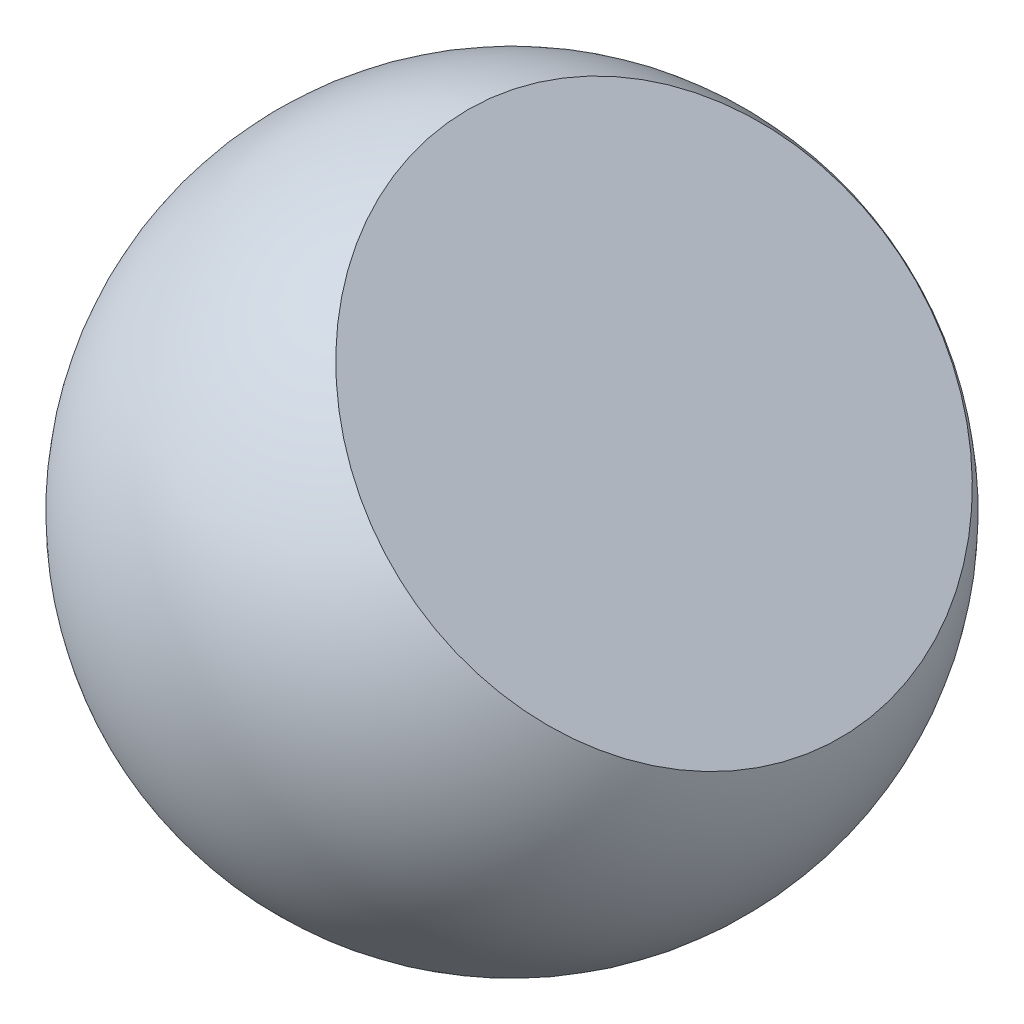
SolidWorks part; units mm, degrees
ref_plane "Front" through (0, 0, 0) normal (0, 0, 1) x (1, 0, 0)
ref_plane "Top" through (0, 0, 0) normal (0, 1, 0) x (1, 0, 0)
ref_plane "Right" through (0, 0, 0) normal (1, 0, 0) x (0, 0, -1)
sketch "Sketch2" plane through (0, 0, 0) normal (0, 1, 0) x (1, 0, 0)
  line L0 (-381, 0) -> (381, 0) construction
  line L1 (-381, 0) -> (381, 0)
  arc A0 (-381, 0) -> (381, 0) centre (0, 0) cw
  dimension "D1" = 762
revolve "Revolve1" add sketch "Sketch2" angle 360 about L0
sketch "Sketch3" plane through (0, 0, 0) normal (0, 0, 1) x (1, 0, 0)
  line L0 (-50.8, 377.5981) -> (381, -38.1) construction
  line L1 (0, 0) -> (164.2276, 170.5889) construction
  line L2 (-50.8, 0) -> (-50.8, 377.5981) construction
  line L3 (381, 0) -> (381, -38.1) construction
  circle A1 centre (0, 0) radius 381 construction
  dimension "D1" = 50.8
  dimension "D2" = 38.1
ref_plane "Plane1" through (164.2276, 170.5889, 0) normal (0.6935, 0.7204, 0) x (-0.7204, 0.6935, 0)
other "SurfaceCut1"
